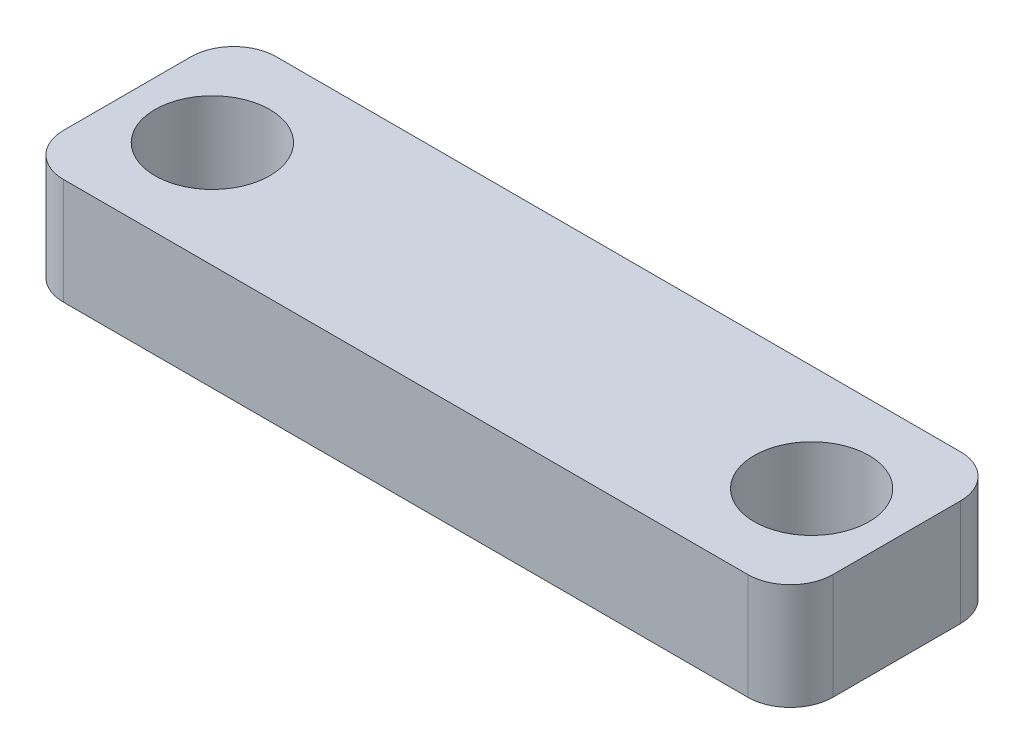
SolidWorks part; units mm, degrees
material "ABS"
ref_plane "Front Plane" through (0, 0, 0) normal (0, 0, 1) x (1, 0, 0)
ref_plane "Top Plane" through (0, 0, 0) normal (0, 1, 0) x (1, 0, 0)
ref_plane "Right Plane" through (0, 0, 0) normal (1, 0, 0) x (0, 0, -1)
sketch "Sketch1" plane through (0, 0, 0) normal (0, 1, 0) x (1, 0, 0)
  line L0 (-7.045, 0) -> (7.045, 0) construction
  line L1 (-9.045, -2.5) -> (9.045, -2.5)
  line L2 (-9.045, -2.5) -> (-9.045, 2.5)
  line L3 (-9.045, 2.5) -> (9.045, 2.5)
  line L4 (9.045, -2.5) -> (9.045, 2.5)
  line L5 (-9.045, -2.5) -> (9.045, 2.5) construction
  line L6 (-9.045, 2.5) -> (9.045, -2.5) construction
  point P0 (0, 0)
  point P9 (0, 0)
  dimension "D1" = 14.09
  dimension "D2" = 5
  dimension "D3" = 2
extrude "Boss-Extrude1" add sketch "Sketch1" along normal blind 2.5
sketch "Sketch2" plane through (0, 0, 0) normal (0, -1, 0) x (-1, 0, 0)
  point P0 (-7.045, 0)
  point P3 (7.045, 0)
hole_wizard "M2.5 Clearance Hole1" positions "Sketch2" profile "Sketch3" hole size "M2.5" standard "ANSI Metric" end condition through all
sketch "Sketch3" plane through (7.045, 0, 0) normal (1, 0, 0) x (0, 0, -1)
  line L0 (0, 0) -> (0, 2.5)
  line L1 (0, 2.5) -> (1.35, 2.5)
  line L2 (1.35, 2.5) -> (1.35, 0)
  line L5 (1.35, 0) -> (0, 0)
  line L11 (0, -6.35) -> (0, 107.95) construction
  dimension "Thru Hole Dia." = 2.7
  dimension "Thru Hole Depth" = 2.5
fillet "Fillet1" radius 1 4 edges at (-9.045, 1.25, 2.5) (9.045, 1.25, 2.5) (-9.045, 1.25, -2.5) (9.045, 1.25, -2.5)
